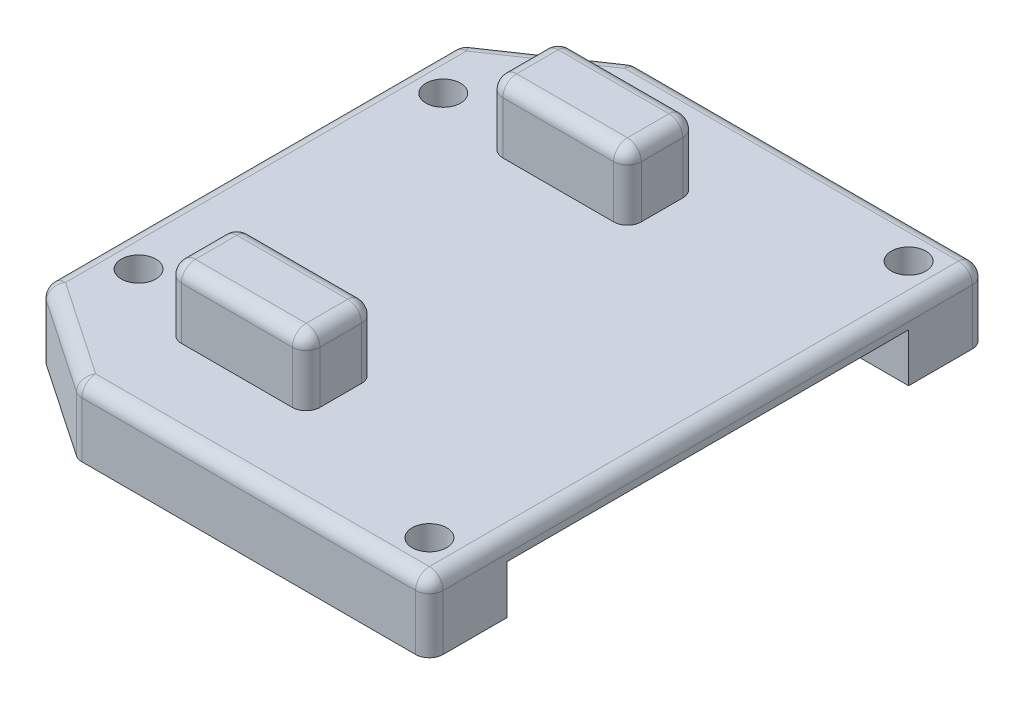
SolidWorks part; units mm, degrees
ref_plane "Front Plane" through (0, 0, 0) normal (0, 0, 1) x (1, 0, 0)
ref_plane "Top Plane" through (0, 0, 0) normal (0, 1, 0) x (1, 0, 0)
ref_plane "Right Plane" through (0, 0, 0) normal (1, 0, 0) x (0, 0, -1)
sketch "Sketch1" plane through (0, 0, 0) normal (0, 1, 0) x (1, 0, 0)
  line L1 (-16.45, -20.1) -> (16.45, -20.1)
  line L2 (-16.45, -20.1) -> (-16.45, 20.1)
  line L3 (-16.45, 20.1) -> (16.45, 20.1)
  line L4 (16.45, -20.1) -> (16.45, 20.1)
  line L5 (-16.45, -20.1) -> (16.45, 20.1) construction
  line L6 (-16.45, 20.1) -> (16.45, -20.1) construction
  point P0 (0, 0)
  dimension "D1" = 40.2
  dimension "D2" = 32.9
extrude "Boss-Extrude1" add sketch "Sketch1" along normal blind 5
sketch "Sketch2" plane through (16.45, 0, 0) normal (1, 0, 0) x (0, 0, -1)
  line L0 (-20.1, 0) -> (20.1, 0) construction
  line L1 (-14.5, 3.5) -> (14.5, 3.5)
  line L2 (-14.5, 3.5) -> (-14.5, 0)
  line L3 (-14.5, 0) -> (14.5, 0)
  line L4 (14.5, 3.5) -> (14.5, 0)
  line L5 (-14.5, 3.5) -> (14.5, 0) construction
  line L6 (-14.5, 0) -> (14.5, 3.5) construction
  point P0 (0, 1.75)
  dimension "D1" = 29
  dimension "D2" = 3.5
extrude "Cut-Extrude1" cut sketch "Sketch2" against normal offset from surface (27.3 mm away) 5.6 up to face at (-16.45, 2.5, 0)
sketch "Sketch3" plane through (0, 5, 0) normal (0, 1, 0) x (1, 0, 0)
  line L0 (16.45, -20.1) -> (16.45, 20.1) construction
  line L1 (16.45, 20.1) -> (-16.45, 20.1) construction
  line L2 (-16.45, 20.1) -> (-16.45, -20.1) construction
  circle A0 centre (13.65, 17.3) radius 1.25
  circle A2 centre (-13.65, 11) radius 1.25
  dimension "D3" = 2.5
  dimension "D1" = 2.8
  dimension "D2" = 2.8
  dimension "D5" = 2.8
  dimension "D6" = 9.1
extrude "Cut-Extrude2" cut sketch "Sketch3" against normal through all
sketch "Sketch4" plane through (0, 5, 0) normal (0, 1, 0) x (-1, 0, 0)
  line L0 (16.45, -20.1) -> (16.45, 20.1) construction
  line L1 (8.45, -14.1) -> (-1.55, -14.1)
  line L2 (8.45, -14.1) -> (8.45, -9.1)
  line L3 (8.45, -9.1) -> (-1.55, -9.1)
  line L4 (-1.55, -14.1) -> (-1.55, -9.1)
  line L5 (8.45, -14.1) -> (-1.55, -9.1) construction
  line L6 (8.45, -9.1) -> (-1.55, -14.1) construction
  line L7 (-16.45, -20.1) -> (16.45, -20.1) construction
  point P0 (3.45, -11.6)
  dimension "D1" = 5
  dimension "D2" = 10
  dimension "D3" = 8
  dimension "D4" = 6
extrude "Boss-Extrude2" add sketch "Sketch4" along normal blind 4.7625
mirror "Mirror1" about plane through (0, 0, 0) normal (0, 0, 1) of "Boss-Extrude2", "Cut-Extrude2"
chamfer "Chamfer1" distance 7.5 distance2 5.1 1 edges at (-16.45, 2.5, -20.1)
chamfer "Chamfer2" distance 5.1 distance2 7.5 1 edges at (-16.45, 2.5, 20.1)
fillet "Fillet1" radius 1 28 edges at (-3.45, 9.7625, 14.1) (-8.45, 9.7625, 11.6) (-3.45, 9.7625, 9.1) (1.55, 9.7625, 11.6) (-3.45, 9.7625, -9.1) (-8.45, 9.7625, -11.6) (-3.45, 9.7625, -14.1) (1.55, 9.7625, -11.6) (16.45, 2.5, -20.1) (16.45, 5, 0) (16.45, 2.5, 20.1) (3.75, 5, 20.1) (-16.45, 5, 0) (-16.45, 2.5, -15) (-8.95, 2.5, -20.1) (-12.7, 5, -17.55) (3.75, 5, -20.1) (1.55, 7.3813, 14.1) (-8.45, 7.3813, 14.1) (1.55, 7.3813, 9.1) (-8.45, 7.3813, 9.1) (1.55, 7.3813, -9.1) (-8.45, 7.3813, -9.1) (1.55, 7.3813, -14.1) (-8.45, 7.3813, -14.1) (-8.95, 2.5, 20.1) (-12.7, 5, 17.55) (-16.45, 2.5, 15)
